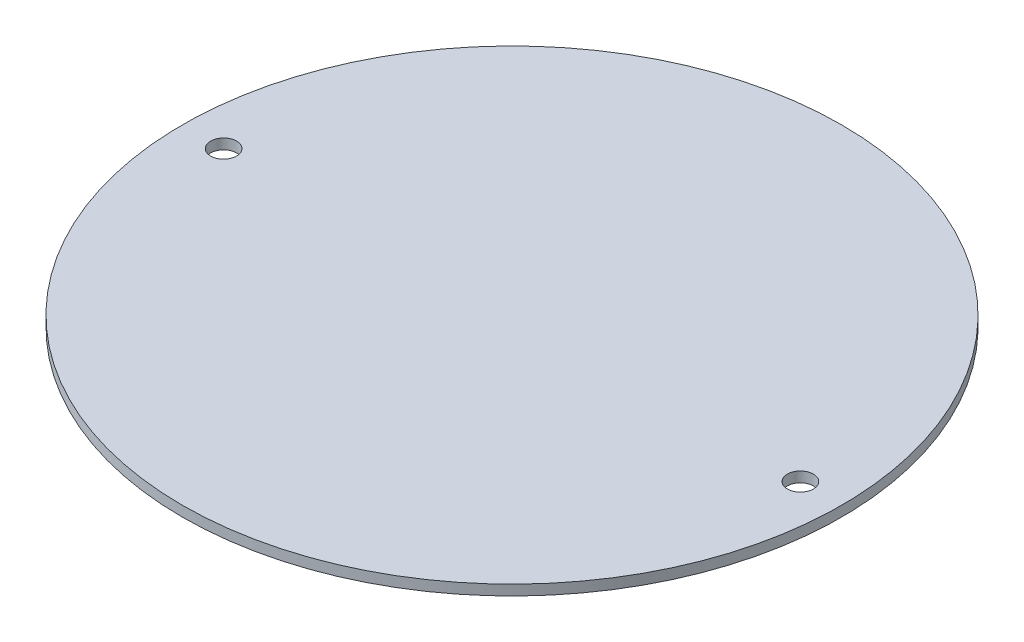
SolidWorks part; units mm, degrees
ref_plane "Front Plane" through (0, 0, 0) normal (0, 0, 1) x (1, 0, 0)
ref_plane "Top Plane" through (0, 0, 0) normal (0, 1, 0) x (1, 0, 0)
ref_plane "Right Plane" through (0, 0, 0) normal (1, 0, 0) x (0, 0, -1)
sketch "Sketch1" plane through (0, 0, 0) normal (0, 1, 0) x (1, 0, 0)
  line L0 (0, 0) -> (22.225, 0) construction
  line L1 (0, 0) -> (-22.225, 0) construction
  circle A0 centre (0, 0) radius 25.4
  circle A1 centre (-22.225, 0) radius 1
  circle A2 centre (22.225, 0) radius 1
  point P7 (-25.4, 0)
  dimension "D1" = 50.8
  dimension "D2" = 2
  dimension "D3" = 3.175
extrude "Boss-Extrude1" add sketch "Sketch1" along normal mid plane 0.7937
